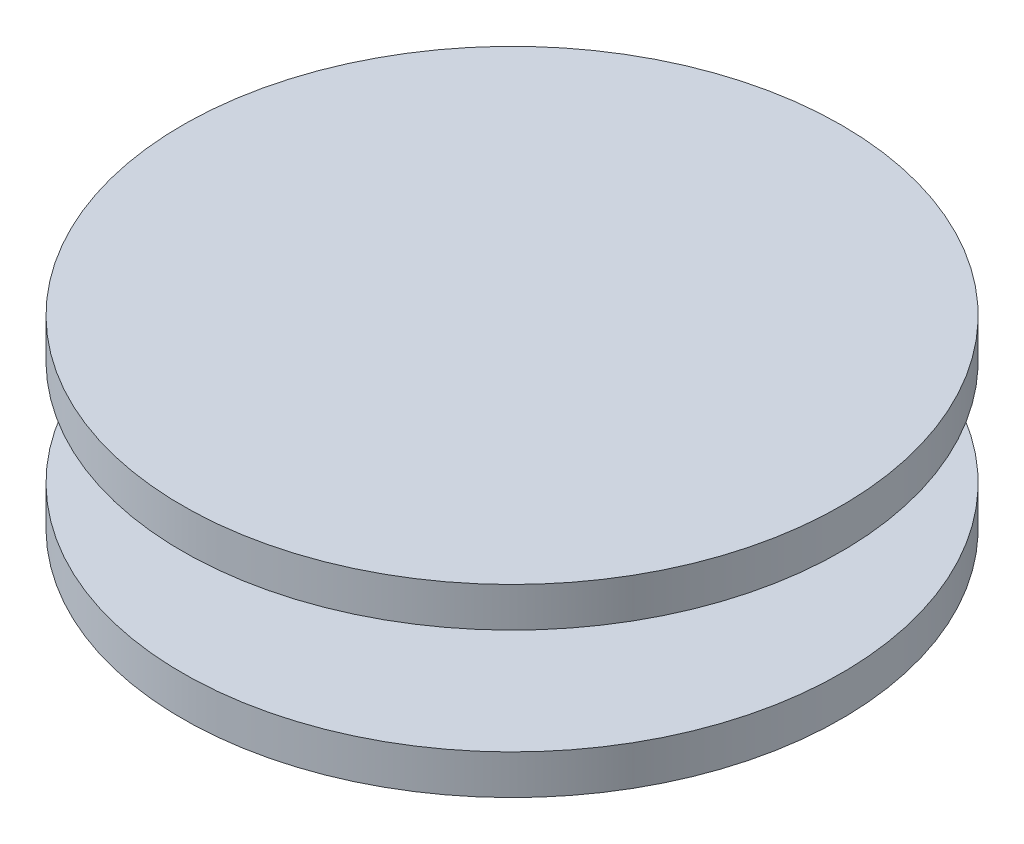
SolidWorks part; units mm, degrees
ref_plane "正面(Front)" through (0, 0, 0) normal (0, 0, 1) x (1, 0, 0)
ref_plane "平面(Top)" through (0, 0, 0) normal (0, 1, 0) x (1, 0, 0)
ref_plane "右側面(Right)" through (0, 0, 0) normal (1, 0, 0) x (0, 0, -1)
sketch "ｽｹｯﾁ1" plane through (0, 0, 0) normal (0, 0, 1) x (1, 0, 0)
  line L0 (0, 0) -> (0, 19.7788) construction
  line L1 (0, 0) -> (25, 0)
  line L2 (25, 0) -> (25, 3)
  line L3 (25, 3) -> (10, 3)
  line L4 (10, 3) -> (10, 11)
  line L5 (10, 11) -> (25, 11)
  line L6 (25, 11) -> (25, 14)
  line L7 (25, 14) -> (0, 14)
  line L8 (0, 0) -> (0, 14)
  dimension "D1" = 10
  dimension "D2" = 25
  dimension "D3" = 8
  dimension "D4" = 3
  dimension "D5" = 3
revolve "回転1" add sketch "ｽｹｯﾁ1" angle 360 about L0
